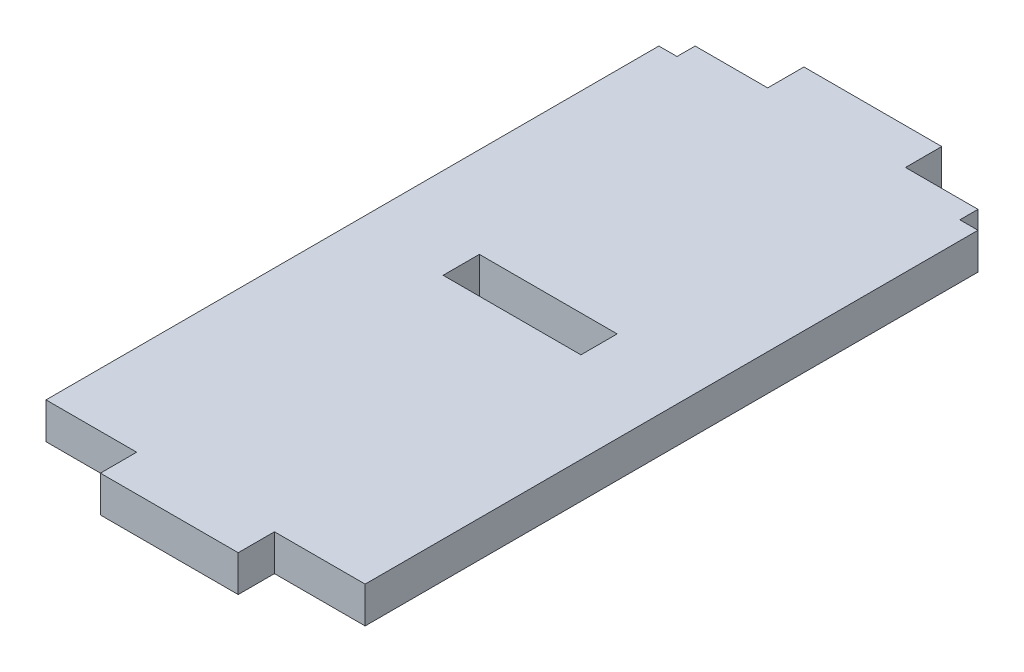
SolidWorks part; units mm, degrees
ref_plane "前视基准面" through (0, 0, 0) normal (0, 0, 1) x (1, 0, 0)
ref_plane "上视基准面" through (0, 0, 0) normal (0, 1, 0) x (1, 0, 0)
ref_plane "右视基准面" through (0, 0, 0) normal (1, 0, 0) x (0, 0, -1)
sketch "草图1" plane through (0, 0, 0) normal (0, 1, 0) x (1, 0, 0)
  line L0 (-2, -2) -> (19.6, -2) construction
  line L1 (0, 0) -> (17.6, 0)
  line L2 (0, 0) -> (0, 34.8)
  line L3 (0, 34.8) -> (17.6, 34.8)
  line L4 (17.6, 0) -> (17.6, 34.8)
  line L5 (19.6, -2) -> (19.6, 36.8) construction
  line L6 (-2, 36.8) -> (19.6, 36.8) construction
  line L7 (-2, -2) -> (-2, 36.8) construction
  line L8 (12.6, 5) -> (12.6, 29.8) construction
  line L9 (5, 29.8) -> (12.6, 29.8) construction
  line L10 (5, 5) -> (5, 29.8) construction
  line L11 (5, 5) -> (12.6, 5) construction
  line L12 (12.6, 5) -> (12.6, -4.6272) construction
  line L13 (5, 5) -> (5, -2) construction
  line L14 (-6.6019, 16.9) -> (28.6178, 16.9) construction
  line L15 (5, 0) -> (12.6, 0)
  line L16 (5, 0) -> (5, -2)
  line L17 (5, -2) -> (12.6, -2)
  line L18 (12.6, 0) -> (12.6, -2)
  line L19 (5, 36.8) -> (12.6, 36.8)
  line L20 (5, 36.8) -> (5, 34.8)
  line L21 (5, 34.8) -> (12.6, 34.8)
  line L22 (12.6, 36.8) -> (12.6, 34.8)
  line L23 (-6.6019, 18.9) -> (28.6178, 18.9) construction
  line L24 (-6.6019, 16.9) -> (28.6178, 16.9) construction
  line L25 (5, 18.9) -> (12.6, 18.9)
  line L26 (5, 18.9) -> (5, 16.9)
  line L27 (5, 16.9) -> (12.6, 16.9)
  line L28 (12.6, 18.9) -> (12.6, 16.9)
  line L30 (0, 34.8) -> (1, 34.8)
  line L31 (0, 34.8) -> (0, 33.8)
  line L32 (0, 33.8) -> (1, 33.8)
  line L33 (1, 34.8) -> (1, 33.8)
  line L34 (17.6, 34.8) -> (16.6, 34.8)
  line L35 (17.6, 34.8) -> (17.6, 33.8)
  line L36 (17.6, 33.8) -> (16.6, 33.8)
  line L37 (16.6, 34.8) -> (16.6, 33.8)
  dimension "D1" = 2
  dimension "D2" = 5
  dimension "D3" = 2
extrude "凸台-拉伸1" add sketch "草图1" along normal blind 2 contours L1 L4 L3 L2 L25 L28 L27 L26 | L18 L1 L16 L17 | L22 L19 L20 L3
